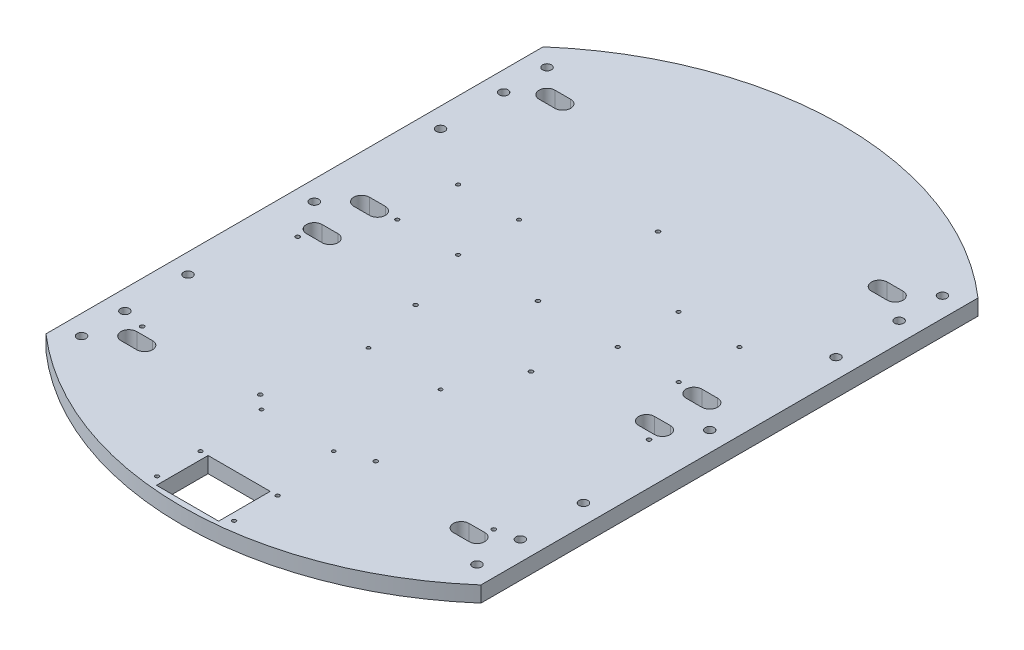
SolidWorks part; units mm, degrees
ref_plane "Front Plane" through (0, 0, 0) normal (0, 0, 1) x (1, 0, 0)
ref_plane "Top Plane" through (0, 0, 0) normal (0, 1, 0) x (1, 0, 0)
ref_plane "Right Plane" through (0, 0, 0) normal (1, 0, 0) x (0, 0, -1)
sketch "Sketch1" plane through (0, 0, 0) normal (0, 1, 0) x (1, 0, 0)
  line L7 (175, -200) -> (-175, -200) construction
  line L16 (175, -200) -> (175, 200)
  line L21 (175, 200) -> (-175, 200) construction
  line L22 (-175, -200) -> (-175, 200)
  line L23 (175, -200) -> (-175, 200) construction
  line L24 (175, 200) -> (-175, -200) construction
  line L27 (0, -264.5751) -> (25, -264.5751) construction
  line L28 (0, -265.7536) -> (0, -264.5751) construction
  line L29 (-25, -261.0751) -> (-25, -219.5751)
  line L30 (-25, -219.5751) -> (25, -219.5751)
  line L31 (25, -219.5751) -> (25, -261.0751)
  line L32 (-25, -264.5751) -> (0, -264.5751) construction
  line L33 (0, -264.5751) -> (0, -219.5751) construction
  line L34 (0, -219.5751) -> (0, 0) construction
  line L35 (-25, -261.0751) -> (25, -261.0751)
  line L36 (-25, -264.5751) -> (-25, -261.0751) construction
  line L37 (25, -261.0751) -> (25, -264.5751) construction
  line L38 (39.5, -170) -> (39.5, -70) construction
  line L39 (39.5, -170) -> (-39.5, -170) construction
  line L40 (-39.5, -170) -> (-39.5, -70) construction
  line L41 (39.5, -70) -> (-39.5, -70) construction
  line L42 (39.5, -170) -> (-39.5, -70) construction
  line L43 (-39.5, -170) -> (39.5, -70) construction
  line L44 (-140.07, -19.05) -> (-127.37, -19.05) construction
  line L45 (-175, -12.7) -> (175, -12.7) construction
  line L46 (-175, -12.7) -> (-175, 12.7) construction
  line L47 (-175, 12.7) -> (175, 12.7) construction
  line L48 (175, -12.7) -> (175, 12.7) construction
  line L49 (-175, -12.7) -> (175, 12.7) construction
  line L50 (-175, 12.7) -> (175, -12.7) construction
  line L51 (-175, -200) -> (-146.42, -200) construction
  line L52 (-175, -200) -> (-175, 200) construction
  line L53 (-175, 200) -> (-146.42, 200) construction
  line L54 (-146.42, -200) -> (-146.42, 200) construction
  line L55 (175, 200) -> (146.42, 200) construction
  line L56 (175, 200) -> (175, -200) construction
  line L57 (175, -200) -> (146.42, -200) construction
  line L58 (146.42, 200) -> (146.42, -200) construction
  line L59 (-140.07, -12.7) -> (-127.37, -12.7)
  line L60 (-140.07, -25.4) -> (-127.37, -25.4)
  line L61 (-140.07, 19.05) -> (-127.37, 19.05) construction
  line L62 (-140.07, 25.4) -> (-127.37, 25.4)
  line L63 (-140.07, 12.7) -> (-127.37, 12.7)
  line L64 (140.07, 19.05) -> (127.37, 19.05) construction
  line L65 (140.07, 25.4) -> (127.37, 25.4)
  line L66 (140.07, 12.7) -> (127.37, 12.7)
  line L67 (140.07, -19.05) -> (127.37, -19.05) construction
  line L68 (140.07, -12.7) -> (127.37, -12.7)
  line L69 (140.07, -25.4) -> (127.37, -25.4)
  line L70 (-140.07, -168.25) -> (-127.37, -168.25) construction
  line L71 (-175, -200) -> (175, -200) construction
  line L72 (-175, -200) -> (-175, -174.6) construction
  line L73 (-175, -174.6) -> (175, -174.6) construction
  line L74 (175, -200) -> (175, -174.6) construction
  line L75 (-175, 200) -> (175, 200) construction
  line L76 (-175, 200) -> (-175, 174.6) construction
  line L77 (-175, 174.6) -> (175, 174.6) construction
  line L78 (175, 200) -> (175, 174.6) construction
  line L79 (-140.07, -161.9) -> (-127.37, -161.9)
  line L80 (-140.07, -174.6) -> (-127.37, -174.6)
  line L81 (127.37, -168.25) -> (140.07, -168.25) construction
  line L82 (127.37, -161.9) -> (140.07, -161.9)
  line L83 (127.37, -174.6) -> (140.07, -174.6)
  line L84 (-140.07, 168.25) -> (-127.37, 168.25) construction
  line L85 (-140.07, 174.6) -> (-127.37, 174.6)
  line L86 (-140.07, 161.9) -> (-127.37, 161.9)
  line L87 (127.37, 168.25) -> (140.07, 168.25) construction
  line L88 (127.37, 174.6) -> (140.07, 174.6)
  line L89 (127.37, 161.9) -> (140.07, 161.9)
  line L114 (-116.42, 73.01) -> (-61.02, 17.7) construction
  line L117 (-116.42, 17.7) -> (-61.02, 17.7) construction
  line L118 (-175, 0) -> (175, 0) construction
  line L120 (-116.42, 17.7) -> (-61.02, 73.01) construction
  line L121 (-116.42, 73.01) -> (-116.42, 17.7) construction
  line L122 (-116.42, 73.01) -> (-61.02, 73.01) construction
  line L125 (-61.02, 73.01) -> (-61.02, 17.7) construction
  line L131 (0, 117.5) -> (0, 20.9) construction
  line L136 (61.02, 73.01) -> (61.02, 17.7) construction
  line L137 (116.42, 73.01) -> (61.02, 73.01) construction
  line L138 (116.42, 17.7) -> (61.02, 73.01) construction
  line L139 (116.42, 17.7) -> (61.02, 17.7) construction
  line L140 (116.42, 73.01) -> (61.02, 17.7) construction
  line L141 (116.42, 73.01) -> (116.42, 17.7) construction
  line L142 (146.42, -26.15) -> (41.42, -161.15) construction
  line L143 (-146.42, -161.15) -> (-41.42, -161.15) construction
  line L144 (-146.42, -161.15) -> (-146.42, -26.15) construction
  line L145 (-146.42, -26.15) -> (-41.42, -26.15) construction
  line L146 (-41.42, -161.15) -> (-41.42, -26.15) construction
  line L147 (-146.42, -161.15) -> (-41.42, -26.15) construction
  line L148 (-146.42, -26.15) -> (-41.42, -161.15) construction
  line L151 (146.42, -161.15) -> (41.42, -26.15) construction
  line L153 (41.42, -161.15) -> (41.42, -26.15) construction
  line L154 (146.42, -26.15) -> (41.42, -26.15) construction
  line L155 (146.42, -161.15) -> (146.42, -26.15) construction
  line L156 (146.42, -161.15) -> (41.42, -161.15) construction
  arc A5 (-175, -200) -> (-25, -264.5751) centre (0, 0) ccw
  arc A6 (-175, 200) -> (-175, -200) centre (0, 0) ccw construction
  arc A8 (175, -200) -> (175, 200) centre (0, 0) ccw construction
  arc A9 (175, 200) -> (-175, 200) centre (0, 0) ccw
  arc A10 (0, -265.7536) -> (25, -264.5751) centre (0, 0) ccw
  arc A11 (25, -264.5751) -> (175, -200) centre (0, 0) ccw
  arc A12 (-25, -264.5751) -> (0, -265.7536) centre (0, 0) ccw
  circle A13 centre (-31, -219.5751) radius 1.5
  circle A14 centre (31, -219.5751) radius 1.5
  circle A15 centre (22.5, -166) radius 1.375
  circle A16 centre (-31, -254.5751) radius 1.5
  circle A17 centre (31, -254.5751) radius 1.5
  circle A18 centre (-35.5, -166) radius 1.375
  circle A19 centre (22.5, -80) radius 1.375
  circle A20 centre (-35.5, -80) radius 1.375
  arc A21 (-140.07, -12.7) -> (-140.07, -25.4) centre (-140.07, -19.05) ccw
  arc A22 (-127.37, -25.4) -> (-127.37, -12.7) centre (-127.37, -19.05) ccw
  arc A23 (-140.07, 25.4) -> (-140.07, 12.7) centre (-140.07, 19.05) ccw
  arc A24 (-127.37, 12.7) -> (-127.37, 25.4) centre (-127.37, 19.05) ccw
  arc A25 (140.07, 25.4) -> (140.07, 12.7) centre (140.07, 19.05) cw
  arc A26 (127.37, 12.7) -> (127.37, 25.4) centre (127.37, 19.05) cw
  arc A27 (140.07, -12.7) -> (140.07, -25.4) centre (140.07, -19.05) cw
  arc A28 (127.37, -25.4) -> (127.37, -12.7) centre (127.37, -19.05) cw
  arc A29 (-140.07, -161.9) -> (-140.07, -174.6) centre (-140.07, -168.25) ccw
  arc A30 (-127.37, -174.6) -> (-127.37, -161.9) centre (-127.37, -168.25) ccw
  arc A31 (127.37, -161.9) -> (127.37, -174.6) centre (127.37, -168.25) ccw
  arc A32 (140.07, -174.6) -> (140.07, -161.9) centre (140.07, -168.25) ccw
  arc A33 (-140.07, 174.6) -> (-140.07, 161.9) centre (-140.07, 168.25) ccw
  arc A34 (-127.37, 161.9) -> (-127.37, 174.6) centre (-127.37, 168.25) ccw
  arc A35 (127.37, 174.6) -> (127.37, 161.9) centre (127.37, 168.25) ccw
  arc A36 (140.07, 161.9) -> (140.07, 174.6) centre (140.07, 168.25) ccw
  circle A53 centre (0, 117.5) radius 1.6
  circle A54 centre (0, 20.9) radius 1.6
  circle A55 centre (-113.22, 20.9) radius 1.5
  circle A56 centre (-64.22, 20.9) radius 1.5
  circle A57 centre (-64.22, 69.81) radius 1.5
  circle A58 centre (-113.22, 69.81) radius 1.5
  circle A63 centre (64.22, 20.9) radius 1.5
  circle A64 centre (113.22, 20.9) radius 1.5
  circle A65 centre (113.22, 69.81) radius 1.5
  circle A66 centre (64.22, 69.81) radius 1.5
  circle A67 centre (-141.42, -31.15) radius 1.625
  circle A68 centre (-46.42, -31.15) radius 1.625
  circle A69 centre (-141.42, -156.15) radius 1.625
  circle A70 centre (-46.42, -156.15) radius 1.625
  circle A81 centre (46.42, -156.15) radius 1.625
  circle A82 centre (141.42, -156.15) radius 1.625
  circle A83 centre (46.42, -31.15) radius 1.625
  circle A84 centre (141.42, -31.15) radius 1.625
  circle A85 centre (-159.12, -101.6) radius 3.5687
  circle A86 centre (-159.12, -152.4) radius 3.5687
  circle A87 centre (-159.12, 152.4) radius 3.5687
  circle A88 centre (-159.12, 101.6) radius 3.5687
  circle A89 centre (159.12, -152.4) radius 3.5687
  circle A90 centre (159.12, -101.6) radius 3.5687
  circle A91 centre (159.12, 101.6) radius 3.5687
  circle A92 centre (159.12, 152.4) radius 3.5687
  circle A93 centre (-159.12, 187.3) radius 3.5687
  circle A94 centre (-159.12, 0) radius 3.5687
  circle A95 centre (-159.12, -187.3) radius 3.5687
  circle A96 centre (159.12, 187.3) radius 3.5687
  circle A97 centre (159.12, 0) radius 3.5687
  circle A98 centre (159.12, -187.3) radius 3.5687
  point P18 (0, -120)
  point P46 (-133.72, -19.05)
  point P53 (-133.72, 19.05)
  point P60 (133.72, 19.05)
  point P67 (133.72, -19.05)
  point P78 (-133.72, -168.25)
  point P86 (133.72, -168.25)
  point P93 (-133.72, 168.25)
  point P100 (133.72, 168.25)
  point P142 (0, 0)
  point P164 (-93.92, -93.65)
  point P200 (93.92, -93.65)
  dimension "D5" = 3
  dimension "D16" = 4
  dimension "D13" = 2.75
  dimension "D28" = 3.2
  dimension "D32" = 3.2
  dimension "D40" = 3.25
  dimension "D45" = 0.75
  dimension "D47" = 101.6
  dimension "D30" = 3
  dimension "D48" = 7.1374
  dimension "D49" = 7.1374
  dimension "D1" = 350
  dimension "D2" = 400
  dimension "D3" = 50
  dimension "D4" = 45
  dimension "D6" = 6
  dimension "D7" = 6
  dimension "D8" = 3.5
  dimension "D9" = 35
  dimension "D10" = 100
  dimension "D11" = 79
  dimension "D12" = 17
  dimension "D14" = 4
  dimension "D15" = 10
  dimension "D17" = 30
  dimension "D18" = 25.4
  dimension "D19" = 28.58
  dimension "D20" = 28.58
  dimension "D21" = 12.7
  dimension "D22" = 12.7
  dimension "D23" = 25.4
  dimension "D24" = 25.4
  dimension "D25" = 30
  dimension "D26" = 55.4
  dimension "D27" = 55.31
  dimension "D29" = 3.2
  dimension "D31" = 3.2
  dimension "D33" = 96.6
  dimension "D34" = 8.2
  dimension "D35" = 5
  dimension "D36" = 3.2
  dimension "D37" = 50.8
  dimension "D38" = 135
  dimension "D39" = 105
  dimension "D41" = 12.7
  dimension "D42" = 5
  dimension "D43" = 5
  dimension "D44" = 5
  dimension "D46" = 5
  dimension "D50" = 12.7
  dimension "D51" = 12.7
  dimension "D52" = 12.7
extrude "Boss-Extrude1" add sketch "Sketch1" along normal blind 12.7
